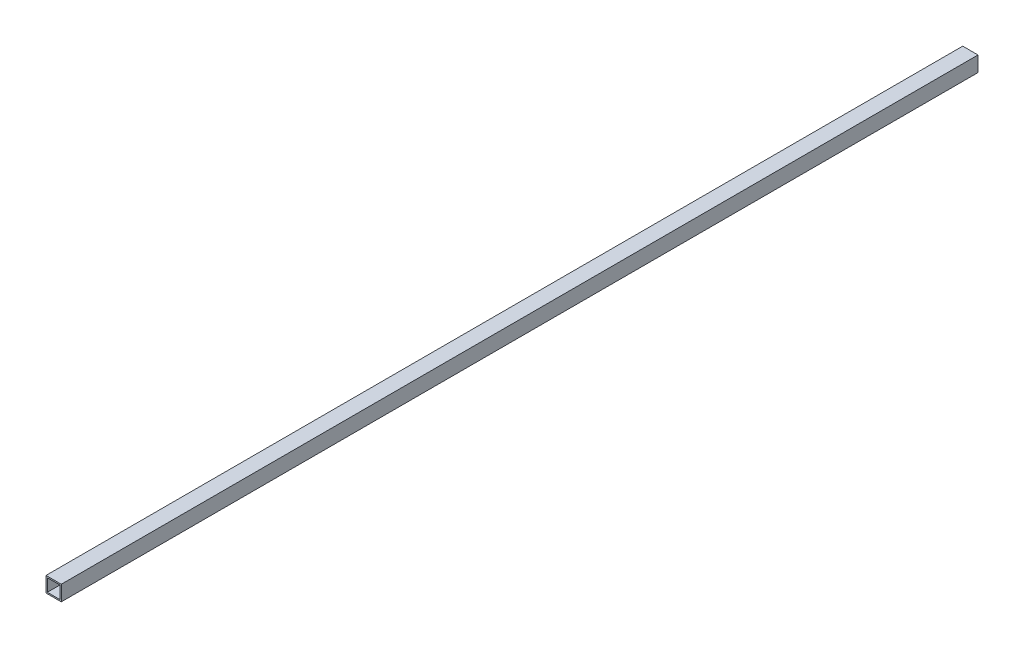
SolidWorks part; units mm, degrees
ref_plane "Спереди" through (0, 0, 0) normal (0, 0, 1) x (1, 0, 0)
ref_plane "Сверху" through (0, 0, 0) normal (0, 1, 0) x (1, 0, 0)
ref_plane "Справа" through (0, 0, 0) normal (1, 0, 0) x (0, 0, -1)
sketch "Эскиз1" plane through (0, 0, 0) normal (0, 0, 1) x (1, 0, 0)
  line L1 (-44.8875, 22.8147) -> (-19.8875, 22.8147)
  line L2 (-44.8875, 22.8147) -> (-44.8875, -2.1853)
  line L3 (-44.8875, -2.1853) -> (-19.8875, -2.1853)
  line L4 (-19.8875, 22.8147) -> (-19.8875, -2.1853)
  dimension "D1" = 25
  dimension "D2" = 25
extrude "Вытянуть-Тонкостенный1" add sketch "Эскиз1" along normal blind 1500 thin
